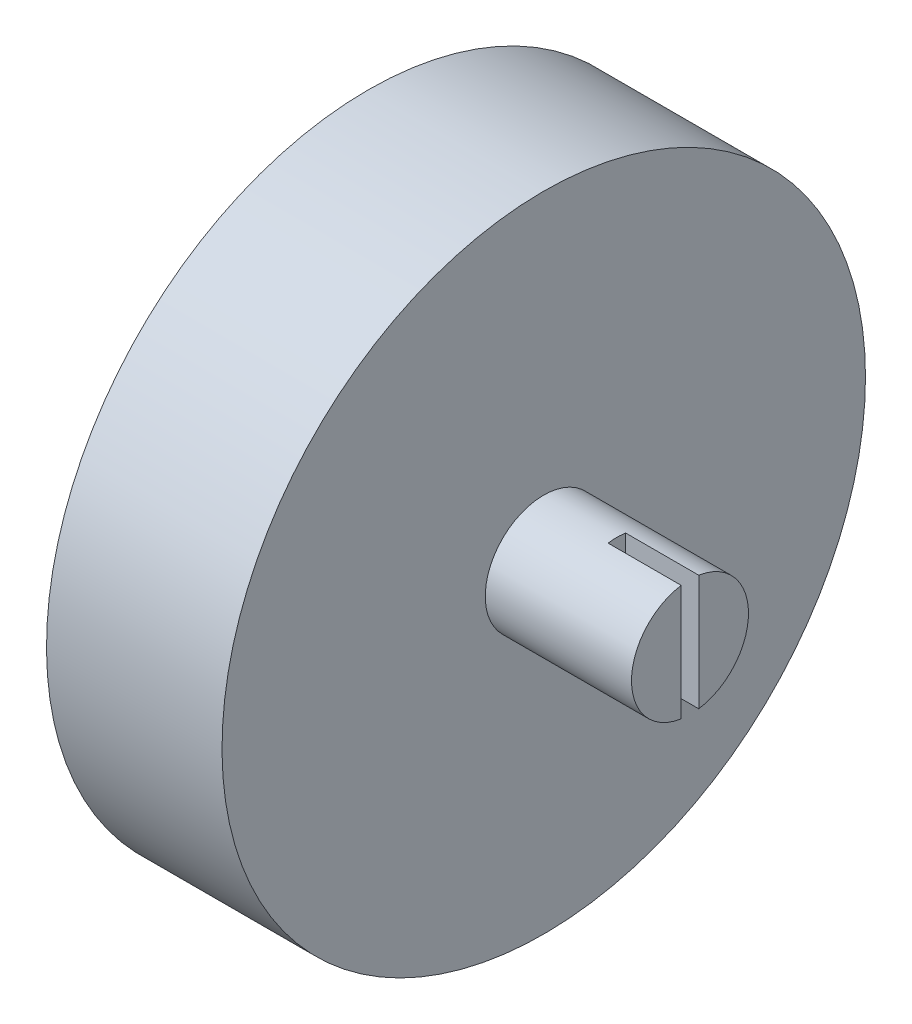
SolidWorks part; units mm, degrees
ref_plane "Front Plane" through (0, 0, 0) normal (0, 0, 1) x (1, 0, 0)
ref_plane "Top Plane" through (0, 0, 0) normal (0, 1, 0) x (1, 0, 0)
ref_plane "Right Plane" through (0, 0, 0) normal (1, 0, 0) x (0, 0, -1)
sketch "Sketch1" plane through (0, 0, 0) normal (1, 0, 0) x (0, 0, -1)
  circle A0 centre (0, 0) radius 22
  dimension "D1" = 44
extrude "Boss-Extrude1" add sketch "Sketch1" along normal blind 12
sketch "Sketch8" plane through (0, 0, 0) normal (1, 0, 0) x (0, 0, -1)
  line L0 (-0.6, -5) -> (0.6, 5) construction
  line L1 (-0.6, 5) -> (0.6, -5) construction
  line L2 (-0.6, -5) -> (0.6, -5)
  line L3 (-0.6, 5) -> (0.6, 5)
  line L4 (-0.6, 5) -> (-0.6, -5)
  line L5 (0.6, -5) -> (0.6, 5)
  point P4 (0, 0)
  dimension "D1" = 1.2
  dimension "D2" = 10
sketch "Sketch13" plane through (0, 0, 0) normal (1, 0, 0) x (0, 0, -1)
  line L0 (-2.6704, -16.8582) -> (-2.6704, -16.5304)
  line L1 (6.5, 19.5569) -> (6.5, -6.9431)
  line L2 (-6.5, 19.5569) -> (-6.5, -6.9431)
  line L3 (0, -25.25) -> (0, 0) construction
  line L4 (2.6704, -16.8582) -> (2.6704, -16.5304)
  line L5 (-4.7624, -10) -> (-2.6704, -16.5304)
  line L6 (0, -25.25) -> (-1.0006, -21.9772)
  line L7 (-6.5, 19.5569) -> (6.5, 19.5569)
  line L8 (-6.5, -6.9431) -> (-4.7624, -6.9431)
  line L9 (6.5, -6.9431) -> (4.7624, -6.9431)
  line L10 (1.0006, -21.9772) -> (0, -25.25)
  line L11 (4.7624, -10) -> (2.6704, -16.5304)
  line L12 (-2.6704, -16.8582) -> (-2.6704, -21.8373)
  line L13 (-4.7624, -10) -> (-4.7624, -6.9431)
  line L14 (4.7624, -10) -> (4.7624, -6.9431)
  line L15 (2.6704, -16.8582) -> (2.6704, -21.8373)
  arc A0 (-2.6704, -21.8373) -> (-1.0006, -21.9772) centre (0, 0) ccw
  arc A1 (1.0006, -21.9772) -> (2.6704, -21.8373) centre (0, 0) ccw
  dimension "D1" = 13
  dimension "D2" = 26.5
  dimension "D3" = 3.0569
  dimension "D4" = 25.25
extrude "Cut-Extrude2" cut sketch "Sketch13" along normal blind 5.5 contours L1 L9 L14 L11 L4 L15 A1 L10 L6 A0 L12 L0 L5 L13 L8 L2 L7
sketch "Sketch15" plane through (0, 0, 0) normal (-1, 0, 0) x (0, 0, 1)
  line L0 (9, 17.1749) -> (9, -6.9431)
  line L1 (9, 17.1749) -> (-9, 17.1749)
  line L2 (9, -6.9431) -> (-9, -6.9431)
  line L3 (0, -6.9431) -> (0, 17.1749) construction
  line L4 (-9, -6.9431) -> (-9, 17.1749)
  line L5 (-6.5, -6.9431) -> (-4.7624, -6.9431) construction
  point P4 (0, -6.9431)
  point P7 (0, 17.1749)
  dimension "D1" = 18
  dimension "D2" = 24.118
extrude "Cut-Extrude3" cut sketch "Sketch15" against normal blind 3
sketch "Sketch16" plane through (12, 0, 0) normal (1, 0, 0) x (0, 0, -1)
  circle A0 centre (0, 0) radius 4
  dimension "D1" = 8
extrude "Boss-Extrude2" add sketch "Sketch16" along normal blind 10
extrude "Cut-Extrude4" cut sketch "Sketch8" against normal blind 5 from surface at 22 starting at face at (22, 0, -4)
sketch "Sketch17" plane through (0, -6.9431, 0) normal (0, 1, 0) x (1, 0, 0)
  line L0 (0, 4.7624) -> (0, 6.5124)
  line L1 (0, 9) -> (0, 4.7624) construction
  line L2 (0, 6.5124) -> (4, 6.5124)
  line L3 (4, 6.5124) -> (4, 4.7624)
  line L4 (5.5, 4.7624) -> (0, 4.7624) construction
  line L5 (4, 4.7624) -> (0, 4.7624)
  dimension "D1" = 1.75
  dimension "D2" = 4
extrude "Boss-Extrude3" add sketch "Sketch17" along normal blind 1
sketch "Sketch18" plane through (0, -6.9431, 0) normal (0, 1, 0) x (1, 0, 0)
  line L0 (5.5, -6.5) -> (3, -6.5) construction
  line L1 (0, -4.7624) -> (4.25, -4.7624)
  line L2 (0, -4.7624) -> (0, -6.5)
  line L3 (0, -6.5) -> (4.25, -6.5)
  line L4 (4.25, -4.7624) -> (4.25, -6.5)
  dimension "D1" = 1.7376
extrude "Boss-Extrude4" add sketch "Sketch18" along normal blind 1
sketch "Sketch22" plane through (0, 0, 0) normal (1, 0, 0) x (0, 0, -1)
  line L0 (0, 0) -> (0, 16.8191) construction
  circle A0 centre (-14, 0) radius 1.5
  circle A1 centre (14, 0) radius 1.5
  dimension "D1" = 3
  dimension "D2" = 14
extrude "Cut-Extrude7" cut sketch "Sketch22" along normal blind 7 from surface at 0 starting at face at (0, 0.1685, -0.0012)
